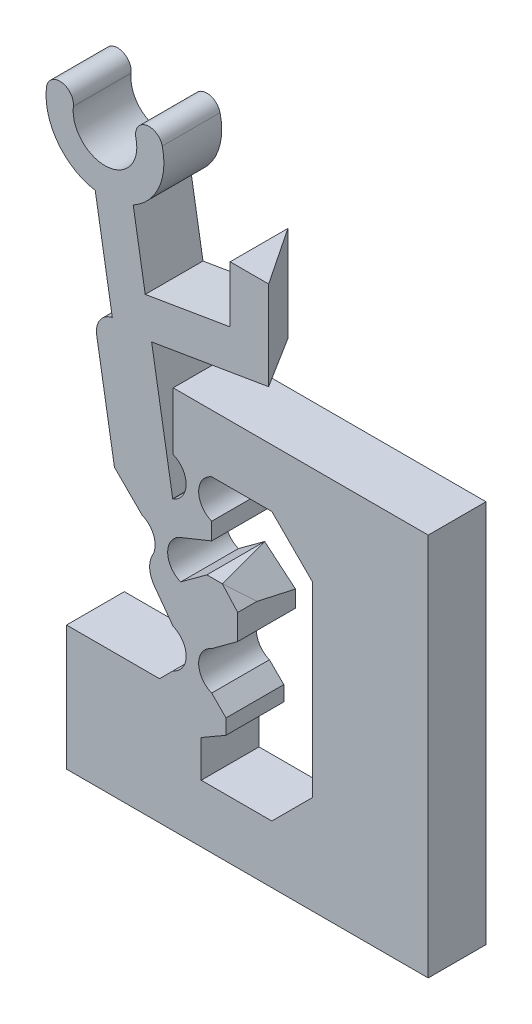
SolidWorks part; units mm, degrees
ref_plane "Front Plane" through (0, 0, 0) normal (0, 0, 1) x (1, 0, 0)
ref_plane "Top Plane" through (0, 0, 0) normal (0, 1, 0) x (1, 0, 0)
ref_plane "Right Plane" through (0, 0, 0) normal (1, 0, 0) x (0, 0, -1)
sketch "Sketch-SkeletonConfigUp" plane through (0, 0, 0) normal (0, 0, 1) x (1, 0, 0)
  line L0 (0, 0) -> (0, -50000) construction
  line L1 (0, 0) -> (4.5811, 6.2164) construction
  line L2 (9.8143, 13.3177) -> (4.5811, 13.945) construction
  line L3 (4.5811, 13.945) -> (2.9713, 10.4094) construction
  line L4 (2.9713, 10.4094) -> (4.5811, 6.2164) construction
  line L5 (4.5811, 13.945) -> (6.2429, 19.1409) construction
  line L6 (2.9713, 10.4094) -> (0.0405, 27.8193) construction
  line L7 (4.5811, 6.2164) -> (9.8143, 13.3177) construction
  line L8 (-587.3593, -797.0242) -> (9.8143, 13.3177) construction
  dimension "D2" = 7.7221
  dimension "D3" = 8.8212
  dimension "D4" = 5.2707
  dimension "D5" = 119.553
  dimension "D6" = 3.8848
  dimension "D7" = 5.4552
  dimension "D8" = 17.6549
  dimension "D9" = 4.4914
  dimension "D10" = 6.745
  dimension "D11" = 145.964
  dimension "D12" = 143.612
sketch "Sketch-SkeletonConfigDown" plane through (0, 0, 0) normal (0, 0, 1) x (1, 0, 0)
  line L0 (0, 0) -> (0, -50000) construction
  line L1 (0, 0) -> (4.5811, 6.2164) construction
  line L2 (9.8143, 13.3177) -> (4.5811, 13.945) construction
  line L3 (4.5811, 13.945) -> (6.1909, 10.4094) construction
  line L4 (6.1909, 10.4094) -> (4.5811, 6.2164) construction
  line L5 (4.5811, 13.945) -> (1.753, 18.6098) construction
  line L6 (6.1909, 10.4094) -> (-8.8652, 19.6294) construction
  line L7 (4.5811, 6.2164) -> (9.8143, 13.3177) construction
  line L8 (-589.9357, -800.5203) -> (9.8143, 13.3177) construction
  dimension "D2" = 7.7221
  dimension "D3" = 8.8212
  dimension "D4" = 5.2707
  dimension "D5" = 119.553
  dimension "D6" = 3.8848
  dimension "D7" = 5.4552
  dimension "D8" = 17.6549
  dimension "D9" = 4.4914
  dimension "D10" = 6.745
  dimension "D11" = 145.964
  dimension "D1" = 143.612
sketch "Sketch-SwitchBossUp" plane through (0, 0, 0) normal (0, 0, 1) x (1, 0, 0)
  line L0 (3.5811, 11.4759) -> (3.5811, 12.945) construction
  line L1 (5.5811, 11.1782) -> (5.5811, 12.0586) construction
  line L2 (6.5405, 22.165) -> (6.5405, 25.0939)
  line L3 (6.5405, 25.0939) -> (8.5405, 25.0939)
  line L4 (8.5405, 25.0939) -> (8.5405, 20.4736)
  line L5 (5.5811, 12.945) -> (5.5811, 12.0586)
  line L7 (1.507, 25.1315) -> (2.1313, 21.4228)
  line L8 (-0.4652, 24.7995) -> (0.4216, 19.5312)
  line L9 (2.9713, 10.4094) -> (0.0405, 27.8193) construction
  line L10 (2.6034, 8.5483) -> (3.5811, 7.2164)
  line L11 (-0.0396, 22.2712) -> (1.9326, 22.6032) construction
  line L15 (4.7006, 8.6678) -> (2.8518, 7.958) construction
  line L16 (2.9713, 10.4094) -> (4.5811, 6.2164) construction
  line L17 (3.5811, 12.945) -> (3.5811, 14.945) construction
  line L18 (5.5811, 12.945) -> (5.5811, 14.945) construction
  line L19 (4.2561, 13.945) -> (4.9061, 13.945) construction
  line L20 (3.5811, 14.945) -> (5.5811, 14.945) construction
  line L21 (3.5811, 12.945) -> (5.5811, 12.945) construction
  line L22 (4.5811, 12.945) -> (4.5811, 14.945) construction
  line L23 (4.5811, 6.2164) -> (8.5405, 7.1023) construction
  line L24 (1.9713, 9.4094) -> (1.9713, 11.4094) construction
  line L25 (3.9713, 9.4094) -> (3.9713, 11.4094) construction
  line L26 (3.9713, 9.4094) -> (1.9713, 9.4094) construction
  line L27 (1.9713, 11.4094) -> (3.9713, 11.4094) construction
  line L28 (3.5811, 7.2164) -> (5.5811, 7.2164) construction
  line L29 (3.5811, 7.2164) -> (3.5811, 5.2164) construction
  line L30 (5.5811, 7.2164) -> (5.5811, 5.2164) construction
  line L31 (3.5811, 5.2164) -> (5.5811, 5.2164) construction
  line L32 (4.9061, 6.2164) -> (4.2561, 6.2164) construction
  line L40 (3.2963, 10.4094) -> (2.6463, 10.4094) construction
  line L43 (2.874, 4.5093) -> (-1.9548, 4.5093)
  line L44 (-1.9548, 4.5093) -> (-1.9548, -1.9756)
  line L45 (-1.9548, -1.9756) -> (5.0405, -1.9756)
  line L46 (5.0405, 1.0244) -> (5.0405, 2.9474)
  line L51 (6.5405, 22.165) -> (2.1313, 21.4228)
  line L61 (6.8113, 14.945) -> (6.8113, 17.945) construction
  line L66 (0.0405, 27.8193) -> (0.0405, 50027.8193) construction
  line L74 (0.5326, 12.848) -> (-0.3888, 18.3216)
  line L75 (0.3841, 13.7302) -> (2.3564, 14.0622) construction
  line L76 (5.5811, 12.0586) -> (5.5811, 12.945) construction
  line L77 (6.7548, 8.2037) -> (5.0019, 8.2037) construction
  line L80 (6.1339, 10.409) -> (6.9354, 9.5189)
  line L81 (8.5405, 7.9632) -> (8.5405, -49992.0368) construction
  line L82 (2.1313, 21.4228) -> (3.5585, 12.945) construction
  line L83 (3.5585, 12.945) -> (2.4634, 19.4505)
  line L84 (2.4634, 19.4505) -> (8.5405, 20.4736)
  line L85 (6.9307, 9.5241) -> (8.5405, 7.7363) construction
  line L86 (5.5811, 7.2164) -> (6.9354, 8.2106)
  line L88 (3.5811, 17.945) -> (6.8113, 17.945)
  line L92 (3.7762, 8.3129) -> (6.9307, 9.5241) construction
  line L93 (6.3271, 3.6903) -> (5.0405, 2.9474)
  line L94 (3.5811, 14.945) -> (3.5811, 17.945)
  line L95 (2.1313, 21.4228) -> (2.4634, 19.4505) construction
  line L96 (2.2974, 20.4367) -> (8.5405, 21.4876) construction
  line L97 (2.2974, 20.4367) -> (1.3112, 20.2707) construction
  line L98 (6.7548, 8.2037) -> (4.7691, 10.409) construction
  line L99 (4.5811, 6.2164) -> (6.1339, 10.409) construction
  line L100 (4.5811, 6.2164) -> (8.5405, 8.2931) construction
  line L101 (4.5811, 6.2164) -> (6.9307, 9.5241) construction
  line L102 (3.5585, 12.945) -> (3.5811, 12.945)
  line L103 (8.5405, 20.4736) -> (8.5405, 8.2931) construction
  line L104 (6.9307, 9.5241) -> (8.5405, 7.7363) construction
  line L106 (6.8113, 14.945) -> (5.5811, 14.945)
  line L107 (1.9713, 9.4094) -> (2.6034, 8.5483) construction
  line L109 (7.3693, 7.7363) -> (8.5405, 7.7363) construction
  line L110 (8.5405, 7.7363) -> (7.3693, 7.7363) construction
  line L111 (6.9354, 9.5189) -> (6.9354, 8.2106)
  line L112 (6.9354, 9.5189) -> (6.9307, 9.5241) construction
  line L114 (7.3693, 7.7363) -> (7.3563, 7.7363) construction
  line L115 (6.8113, 17.945) -> (16.8281, 17.945)
  line L116 (16.8281, 17.945) -> (16.8281, -1.9756)
  line L117 (16.8281, -1.9756) -> (5.0405, -1.9756)
  line L118 (6.8113, 14.945) -> (8.7068, 14.945)
  line L119 (10.8281, 12.8236) -> (10.8281, 3.1457)
  line L120 (8.7068, 1.0244) -> (5.0405, 1.0244)
  line L121 (5.0405, -1.9756) -> (5.0405, 1.0244) construction
  line L122 (10.8281, 14.945) -> (13.8281, 14.945) construction
  line L123 (13.8281, 14.945) -> (16.8281, 14.945) construction
  line L124 (10.8281, 3.1457) -> (8.7068, 1.0244)
  line L125 (10.8281, 7.9847) -> (16.8281, 7.9847) construction
  line L126 (10.8281, 12.8236) -> (8.7068, 14.945)
  line L127 (8.5405, 14.945) -> (10.8281, 14.945) construction
  line L128 (10.8281, 14.945) -> (10.8281, 12.8236) construction
  line L129 (10.8281, 3.1457) -> (10.8281, 1.0244) construction
  line L130 (10.8281, 1.0244) -> (8.7068, 1.0244) construction
  line L133 (2.9713, 10.4094) -> (6.1909, 10.4094) construction
  line L134 (4.5811, 10.4094) -> (4.5811, 13.945) construction
  line L135 (4.5811, 10.4094) -> (4.5811, 6.2164) construction
  line L136 (1.9713, 11.4094) -> (0.5326, 12.848)
  line L137 (3.9713, 9.4094) -> (5.5811, 7.2164) construction
  line L138 (3.5811, 5.2164) -> (2.874, 4.5093)
  line L139 (5.333, 10.409) -> (3.9713, 9.4094)
  line L143 (4.7691, 10.409) -> (5.333, 10.409) construction
  line L144 (5.333, 10.409) -> (6.1339, 10.409)
  line L145 (4.5811, 10.4534) -> (4.7691, 10.409) construction
  line L146 (3.9713, 11.4094) -> (5.5811, 12.0586)
  line L147 (5.5811, 12.0586) -> (5.5811, 12.945) construction
  line L148 (5.5811, 5.2164) -> (6.3271, 4.4705)
  line L149 (6.3271, 4.4705) -> (6.3271, 3.6903)
  arc A0 (1.507, 25.1315) -> (3.0168, 28.5383) centre (0.0405, 27.8193) ccw
  arc A1 (-0.4652, 24.7995) -> (-3.0011, 28.1713) centre (0.0405, 27.8193) cw
  arc A2 (-3.0011, 28.1713) -> (-1.6023, 28.0095) centre (-2.3017, 28.0904) cw
  arc A3 (3.0168, 28.5383) -> (1.648, 28.2077) centre (2.3324, 28.373) ccw
  arc A4 (-1.6023, 28.0095) -> (1.648, 28.2077) centre (0.0405, 27.8193) ccw
  arc A5 (3.5811, 12.945) -> (3.5811, 14.945) centre (3.1778, 13.945) ccw
  arc A6 (5.5811, 12.945) -> (5.5811, 14.945) centre (5.9843, 13.945) cw
  arc A7 (2.5141, 9.892) -> (1.9713, 11.4094) centre (1.568, 10.4094) ccw
  arc A8 (3.9713, 11.4094) -> (3.9713, 9.4094) centre (4.3745, 10.4094) ccw
  arc A9 (3.5811, 7.2164) -> (3.5811, 5.2164) centre (3.1779, 6.2164) cw
  arc A10 (5.5811, 7.2164) -> (5.5811, 5.2164) centre (5.9844, 6.2164) ccw
  arc A19 (-0.3888, 18.3216) -> (0.4216, 19.5312) centre (0.6565, 18.4975) cw
  arc A27 (2.5141, 9.892) -> (2.6034, 8.5483) centre (3.6143, 9.2904) ccw
  arc A28 (6.21, 3.6227) -> (5.2269, 3.6539) centre (5.7492, 4.6041) cw construction
  arc A29 (1.9713, 9.4094) -> (2.5141, 9.892) centre (1.568, 10.4094) ccw construction
  point P35 (0, 0)
  point P44 (3.7762, 8.3129)
  point P53 (4.5811, 13.945)
  point P54 (2.8518, 4.4705)
  point P63 (2.9713, 10.4094)
  point P93 (0.9465, 22.4372)
  dimension "D1" = 2
  dimension "D2" = 2
  dimension "D3" = 2
  dimension "D4" = 3
  dimension "D5" = 2
  dimension "D6" = 0.65
  dimension "D7" = 2
  dimension "D8" = 42
  dimension "D9" = 3
  dimension "D10" = 5
  dimension "D11" = 8.5
  dimension "D12" = 120
  dimension "D14" = 10
  dimension "D15" = 45
  dimension "D16" = 42
  dimension "D18" = 3
  dimension "D19" = 135
  dimension "D20" = 135
  dimension "D21" = 1
  dimension "D22" = 135
extrude "Boss-SwitchMain" add sketch "Sketch-SwitchBossUp" along normal blind 3
sketch "Sketch1" plane through (0, 0, 0) normal (0, 0, -1) x (-1, 0, 0)
  line L0 (1.9548, 4.5093) -> (1.9548, -1.9756) construction
  line L1 (-4.628, -1.1895) -> (1.9548, -1.1895)
  line L2 (-4.628, -1.1895) -> (-4.628, 0.3105)
  line L3 (-4.628, 0.3105) -> (1.9548, 0.3105)
  line L4 (1.9548, -1.1895) -> (1.9548, 0.3105)
  line L5 (-3.5811, 17.945) -> (-6.6395, 17.945)
  line L6 (-2.5363, 4.5093) -> (1.9548, 4.5093)
  line L7 (-2.5363, 4.5093) -> (-2.5363, 3.0093)
  line L8 (-2.5363, 3.0093) -> (1.9548, 3.0093)
  line L9 (1.9548, 4.5093) -> (1.9548, 3.0093)
  line L10 (-6.6395, 17.945) -> (-6.8113, 16.4548)
  line L11 (-2.874, 4.5093) -> (1.9548, 4.5093) construction
  line L12 (-6.8113, 16.4548) -> (-3.5811, 16.4548)
  line L13 (-5.128, -1.3839) -> (-5.128, 7.6731) construction
  line L14 (-3.5811, 16.4548) -> (-3.5811, 17.945)
  line L18 (-3.5811, 17.945) -> (-3.5811, 14.945) construction
  line L19 (-5.128, -1.3839) -> (-5.128, 7.6731) construction
  line L20 (-6.8113, 17.945) -> (-16.8281, 17.945) construction
  line L21 (-6.8113, 14.945) -> (-6.8113, 17.945) construction
  dimension "D1" = 1.5
  dimension "D2" = 1.5
  dimension "D3" = 1.5
  dimension "D4" = 0.5
extrude "Boss-Flange Width" add sketch "Sketch1" along normal blind 6
ref_plane "Plane-Sta2Sit Groove" through (0.0405, 0, 0) normal (1, 0, 0) x (0, 0, -1)
ref_plane "Plane-Cam Face" through (-12.0395, 0, 0) normal (1, 0, 0) x (0, 0, -1)
ref_plane "Plane-FlangeTop" through (-7.0395, 0, 0) normal (1, 0, 0) x (0, 0, -1)
sketch "Sketch2" plane through (-7.0395, 0, 0) normal (1, 0, 0) x (0, 0, -1)
  line L0 (6, 16.4548) -> (0, 16.4548) construction
  line L1 (6, 17.945) -> (1, 17.945)
  line L2 (6, 17.945) -> (6, 16.4548)
  line L3 (6, 16.4548) -> (1, 16.4548)
  line L4 (1, 17.945) -> (1, 16.4548)
  line L5 (6, 3.0093) -> (0, 3.0093) construction
  line L6 (6, 4.5093) -> (1, 4.5093)
  line L7 (6, 4.5093) -> (6, 3.0093)
  line L8 (6, 3.0093) -> (1, 3.0093)
  line L9 (1, 4.5093) -> (1, 3.0093)
  line L10 (-3, -1.9756) -> (0, -1.9756) construction
  line L11 (6, 0.3105) -> (1, 0.3105)
  line L12 (6, 0.3105) -> (6, -1.9756)
  line L13 (6, -1.9756) -> (1, -1.9756)
  line L14 (1, 0.3105) -> (1, -1.9756)
  line L15 (0, 10.4094) -> (0, 27.8193) construction
  dimension "D1" = 1
extrude "Boss-Flange Height" add sketch "Sketch2" along normal up to surface (11.6675 mm away)
sketch "Sketch-HolePositions" plane through (0, -1.9756, 0) normal (0, -1, 0) x (1, 0, 0)
  line L0 (-7.0395, -3.5) -> (4.628, -3.5) construction
  line L2 (4.628, -1) -> (4.628, 0) construction
  line L3 (4.628, -1) -> (-7.0395, -1) construction
  line L4 (-7.0395, -22.2167) -> (-7.0395, 22.2167) construction
  point P6 (-4.0395, -3.5)
  point P7 (1.628, -3.5)
  dimension "D1" = 3
  dimension "D2" = 3
  dimension "D3" = 2.5
sketch "Sketch6" plane through (0, -1.9756, 0) normal (0, -1, 0) x (-1, 0, 0)
  point P0 (4.0395, 3.5)
  point P3 (-1.628, 3.5)
hole_wizard "Tap Drill for M2x0.4 Tap1" positions "Sketch6" profile "Sketch5" hole size "M2x0.4" standard "ANSI Metric" end condition through all
sketch "Sketch5" plane through (-4.0395, -1.9756, -3.5) normal (1, 0, 0) x (0, 0, -1)
  line L0 (0, 0) -> (0, 31.0527)
  line L1 (0, 31.0527) -> (0.8, 31.0527)
  line L2 (0.8, 31.0527) -> (0.8, 0)
  line L5 (0.8, 0) -> (0, 0)
  line L11 (0, -6.35) -> (0, 107.95) construction
  dimension "Thru Hole Dia." = 1.6
  dimension "Thru Hole Depth" = 31.0527
sketch "Sketch9" plane through (0, -1.9756, 0) normal (0, -1, 0) x (1, 0, 0)
  point P0 (-4.0395, -3.5)
  point P3 (1.628, -3.5)
hole_wizard "M2 Clearance Hole2" positions "Sketch9" profile "Sketch8" hole size "M2" standard "ANSI Metric"
sketch "Sketch8" plane through (-4.0395, -1.9756, -3.5) normal (1, 0, 0) x (0, 0, -1)
  line L0 (0, 0) -> (0, 7.206)
  line L1 (0, 7.206) -> (1.2, 6.4849)
  line L2 (1.2, 6.4849) -> (1.2, 0)
  line L5 (1.2, 0) -> (0, 0)
  line L10 (0, 7.206) -> (-1.2, 6.4849) construction
  line L11 (0, -6.35) -> (0, 107.95) construction
  dimension "Hole Dia." = 2.4
  dimension "Hole Depth" = 6.4849
  dimension "Drill Angle" = 118
sketch "Sketch10" plane through (0, 17.945, 0) normal (0, 1, 0) x (1, 0, 0)
  line L1 (6.6395, 6) -> (5.128, 6)
  line L2 (6.6395, 6) -> (6.6395, 3)
  line L3 (6.6395, 3) -> (5.128, 3)
  line L5 (4.628, 7) -> (4.628, 1) construction
  line L6 (3.5811, 1) -> (-7.0395, 1) construction
  line L7 (5.128, 6.25) -> (5.128, 1) construction
  line L8 (5.128, 6) -> (5.128, 3)
  dimension "D1" = 2
extrude "Cut-Flange Ramp Clearance" cut sketch "Sketch10" against normal up to next
sketch "Sketch-Measurements for Derailleur Ramps" plane through (0, 0, 0) normal (0, 0, 1) x (1, 0, 0)
  line L0 (2.4634, 19.4505) -> (2.1313, 21.4228)
  line L1 (2.2974, 20.4367) -> (1.3112, 20.2707)
  line L2 (2.9713, 10.4094) -> (0.0405, 27.8193) construction
  line L3 (1.3112, 20.2707) -> (-4.0257, 16.6658)
  line L4 (6.1909, 10.4094) -> (-8.8652, 19.6294) construction
  line L5 (1.3112, 20.2707) -> (2.6012, 12.6077)
  line L6 (2.6012, 12.6077) -> (-4.0257, 16.6658)
  line L7 (-1.3573, 18.4682) -> (-1.3573, 20.2707)
  line L8 (-1.3573, 20.2707) -> (1.3112, 20.2707)
  line L9 (6.1909, 10.4094) -> (2.9713, 10.4094)
  line L10 (5.386, 8.3129) -> (3.7762, 8.3129)
  line L12 (6.1909, 10.4094) -> (4.5811, 6.2164) construction
  line L13 (4.5811, 8.3129) -> (4.5811, 8.7912)
  line L14 (4.5811, 6.2164) -> (5.386, 8.3129)
  line L15 (2.9713, 10.4094) -> (4.5811, 6.2164) construction
  line L16 (3.7762, 8.3129) -> (4.5811, 6.2164)
  line L17 (5.386, 8.3129) -> (5.386, 8.7912)
  dimension "D1" = 2.6685
  dimension "D2" = 0.8049
sketch "Sketch12" plane through (0, 25.0939, 0) normal (0, 1, 0) x (1, 0, 0)
  line L0 (6.5405, 0) -> (8.5405, -3)
  line L1 (8.5405, -3) -> (8.5405, 0)
  line L2 (8.5405, 0) -> (6.5405, 0)
extrude "Cut-Extrude1" cut sketch "Sketch12" against normal up to next
ref_plane "Plane1" through (0, 7.1023, 0) normal (0, 1, 0) x (1, 0, 0)
sketch "Sketch-Derailleur Location" plane through (0, 7.1023, 0) normal (0, 1, 0) x (1, 0, 0)
  line L0 (8.5405, 0) -> (8.5405, -3)
  line L1 (3.5811, -3) -> (4.2561, -3) construction
  line L2 (-119237.4187, 0) -> (9.8143, 0) construction
  point P0 (8.5405, 0)
  point P8 (8.5405, -1.5)
ref_plane "Plane-Cantilever Cut" through (7.0973, 8.5173, -1.8949) normal (-0.631, -0.7573, 0.1685) x (-0.7758, 0.616, -0.137)
sketch "Sketch14" plane through (7.0973, 8.5173, -1.8949) normal (-0.631, -0.7573, 0.1685) x (-0.7758, 0.616, -0.137)
  line L0 (2.5653, -1.6911) -> (-0.4368, -1.6911)
  line L2 (2.5653, -5.3731) -> (2.5653, -1.6911)
  line L3 (-0.4368, -1.6911) -> (-0.4368, -5.3731)
  line L4 (-0.4368, -5.3731) -> (2.5653, -5.3731)
extrude "Cut-Extrude2" cut sketch "Sketch14" against normal up to next
sketch "Sketch15" plane through (0, 0, 0) normal (0, 0, -1) x (-1, 0, 0)
  line L1 (-10.0534, 18.2157) -> (8.3706, 18.2157)
  line L2 (-10.0534, 18.2157) -> (-10.0534, -2.1599)
  line L3 (-10.0534, -2.1599) -> (8.3706, -2.1599)
  line L4 (8.3706, 18.2157) -> (8.3706, -2.1599)
extrude "Cut-Extrude3" cut sketch "Sketch15" along normal through all
equation "\"axle-diameter\"=2"
equation "\"switch-thickness\"=12"
equation "\"base-width\"=4.0"
equation "\"axle-bushing-radius\"=3"
equation "\"clearance\"= 0.25"
equation "\"arm-width\"=1.5"
equation "\"min-diameter\"=70"
equation "\"alpha\"=143.6120"
equation "\"gamma\"=119.5526"
equation "\"delta\"=145.9637"
equation "\"epsilon\"=6.7452"
equation "\"l_AB\"=8.8212"
equation "\"l_AC\"=4.4914"
equation "\"l_BD\"=5.2707"
equation "\"l_CD\"=3.8848"
equation "\"l_CE\"=17.6549"
equation "\"l_DF\"=5.4552"
equation "\"l_OA\"=7.7221"
equation "\"D2@Sketch-SkeletonConfigUp\" = \"l_OA\""
equation "\"D3@Sketch-SkeletonConfigUp\" = \"l_AB\""
equation "\"D4@Sketch-SkeletonConfigUp\" = \"l_BD\""
equation "\"D5@Sketch-SkeletonConfigUp\" = \"gamma\""
equation "\"D6@Sketch-SkeletonConfigUp\" = \"l_CD\""
equation "\"D7@Sketch-SkeletonConfigUp\" = \"l_DF\""
equation "\"D8@Sketch-SkeletonConfigUp\" = \"l_CE\""
equation "\"D9@Sketch-SkeletonConfigUp\" = \"l_AC\""
equation "\"D_groove\"=3.175"
equation "\"D7@Sketch-SkeletonConfigDown\" = \"l_DF\""
equation "\"D6@Sketch-SkeletonConfigDown\" = \"l_CD\""
equation "\"D2@Sketch-SkeletonConfigDown\" = \"l_OA\""
equation "\"D3@Sketch-SkeletonConfigDown\" = \"l_AB\""
equation "\"D9@Sketch-SkeletonConfigDown\" = \"l_AC\""
equation "\"D8@Sketch-SkeletonConfigDown\" = \"l_CE\""
equation "\"D5@Sketch-SkeletonConfigDown\" = \"gamma\""
equation "\"D4@Sketch-SkeletonConfigDown\" = \"l_BD\""
equation "\"D1@Sketch-SkeletonConfigDown\" = \"alpha\""
equation "\"hinge_length\"=1.5"
equation "\"hinge_depth\"=0.25"
equation "\"D10@Sketch-SkeletonConfigUp\"=\"epsilon\""
equation "\"D11@Sketch-SkeletonConfigUp\"=\"delta\""
equation "\"D12@Sketch-SkeletonConfigUp\"=\"alpha\""
equation "\"D11@Sketch-SkeletonConfigDown\"=\"delta\""
equation "\"D10@Sketch-SkeletonConfigDown\"=\"epsilon\""
equation "\"EE_dx\"=8.9056"
equation "\"EE_dy\"=8.1898"
equation "\"r_groove\"=\"D_groove\"/2"
equation "\"t_wall\"=25.4/16"
equation "\"width_lower\"=\"D_groove\"+\"t_wall\""
equation "\"cable_to_bottom\"=30.6257"
equation "\"switch_EE-up_base_dy\"=24"
equation "\"switch_EE-down_base_dy\"=16"
equation "\"D_axle\"=25.4/8"
equation "\"D_up_to_down\"=16"
equation "\"D_down_to_up\"=25"
equation "\"t_cam_base\"=7.5"
